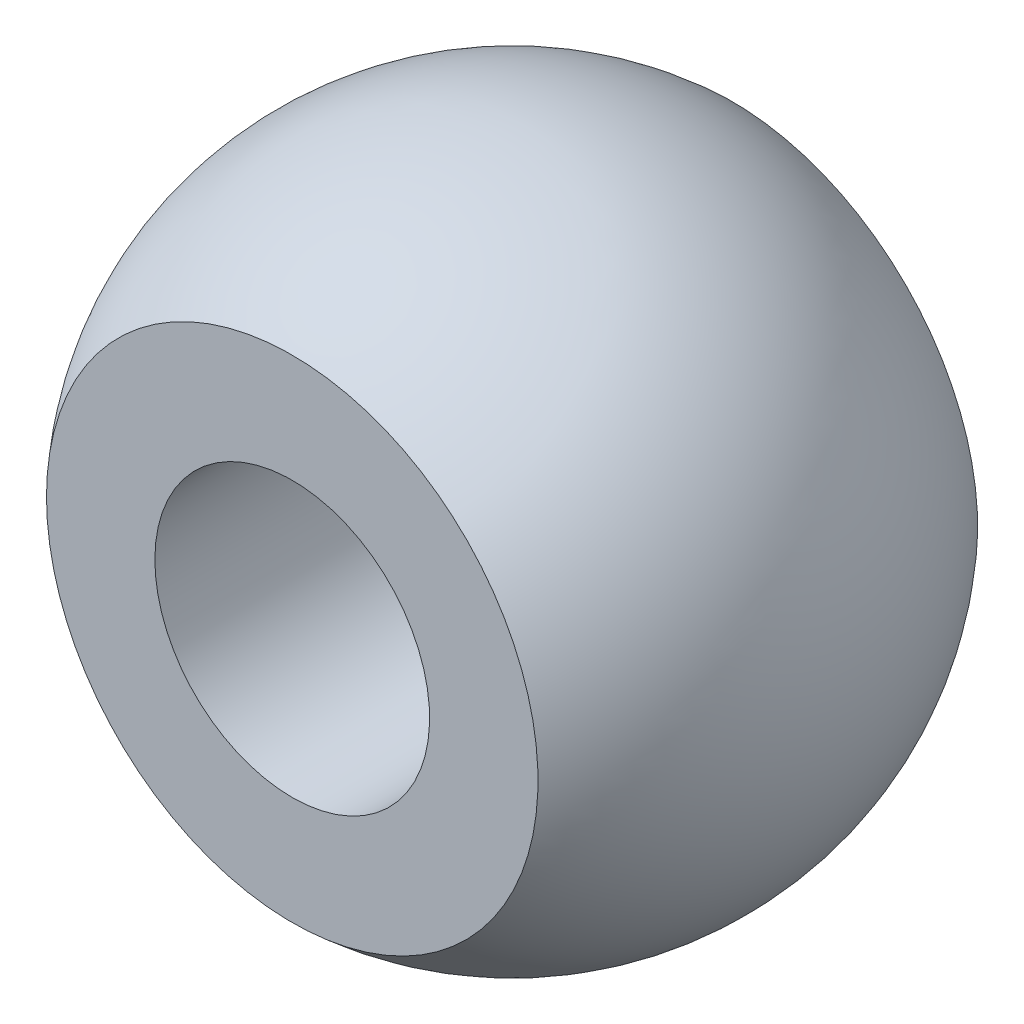
SolidWorks part; units mm, degrees
ref_plane "Alzado" through (0, 0, 0) normal (0, 0, 1) x (1, 0, 0)
ref_plane "Planta" through (0, 0, 0) normal (0, 1, 0) x (1, 0, 0)
ref_plane "Vista lateral" through (0, 0, 0) normal (1, 0, 0) x (0, 0, -1)
sketch "Croquis1" plane through (0, 0, 0) normal (0, 0, 1) x (1, 0, 0)
  line L0 (0, 6) -> (0, -6)
  arc A0 (0, 6) -> (0, -6) centre (0, 0) ccw
  dimension "EsferaE" = 12
revolve "Revolución1" add sketch "Croquis1" angle 360 about L0
sketch "Croquis2" plane through (0, 0, 0) normal (0, 0, 1) x (1, 0, 0)
  circle A0 centre (0, 0) radius 2.5
  dimension "B" = 5
extrude "Cortar-Extruir1" cut sketch "Croquis2" against normal through all both and the other way through all
sketch "Croquis3" plane through (0, 0, 0) normal (1, 0, 0) x (0, 0, -1)
  line L0 (-4, 0) -> (4, 0) construction
  line L1 (-4, -4.4721) -> (-4, 4.4721)
  line L2 (-14, -4.4721) -> (-14, 4.4721)
  line L3 (-4, 4.4721) -> (-14, 4.4721)
  line L4 (-4, -4.4721) -> (-14, -4.4721)
  line L5 (0, -1000) -> (0, 49000) construction
  line L6 (4, -4.4721) -> (4, 4.4721)
  line L7 (4, 4.4721) -> (14, 4.4721)
  line L8 (14, -4.4721) -> (14, 4.4721)
  line L9 (4, -4.4721) -> (14, -4.4721)
  arc A0 (5.4544, 2.5) -> (-5.4544, 2.5) centre (0, 0) ccw construction
  point P4 (0, 0)
  point P11 (-4, 0)
  dimension "D1" = 10
  dimension "W" = 8
extrude "Cortar-Extruir2" cut sketch "Croquis3" against normal through all both and the other way through all
